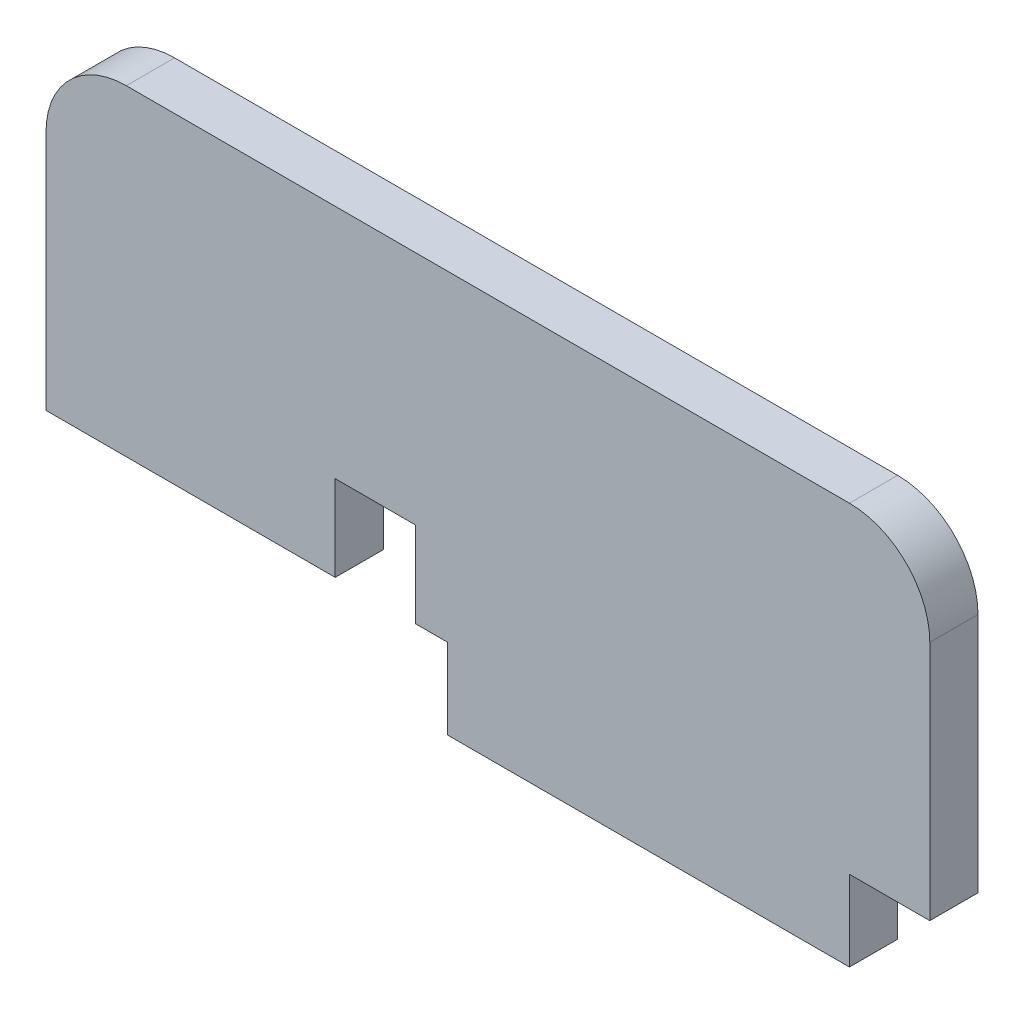
SolidWorks part; units mm, degrees
ref_plane "Plano frontal" through (0, 0, 0) normal (0, 0, 1) x (1, 0, 0)
ref_plane "Plano superior" through (0, 0, 0) normal (0, 1, 0) x (1, 0, 0)
ref_plane "Plano direito" through (0, 0, 0) normal (1, 0, 0) x (0, 0, -1)
sketch "Esboço1" plane through (0, 0, 0) normal (0, 0, 1) x (1, 0, 0)
  line L0 (-7.9412, 1.3698) -> (-2.9412, 1.3698)
  line L1 (-52.9412, 21.3698) -> (-7.9412, 21.3698)
  line L2 (-57.9412, 16.3698) -> (-57.9412, 1.3698)
  line L3 (-57.9412, 1.3698) -> (-32.9412, 1.3698)
  line L4 (-2.9412, 16.3698) -> (-2.9412, 1.3698)
  line L6 (-32.9412, 1.3698) -> (-32.9412, -3.6302)
  line L7 (-32.9412, -3.6302) -> (-7.9412, -3.6302)
  line L8 (-7.9412, 1.3698) -> (-7.9412, -3.6302)
  arc A0 (-7.9412, 21.3698) -> (-2.9412, 16.3698) centre (-7.9412, 16.3698) cw
  arc A1 (-52.9412, 21.3698) -> (-57.9412, 16.3698) centre (-52.9412, 16.3698) ccw
  point P10 (-2.9412, 21.3698)
  point P13 (-57.9412, 21.3698)
  dimension "D6" = 5
  dimension "D1" = 20
  dimension "D2" = 55
  dimension "D3" = 5
  dimension "D4" = 25
  dimension "D5" = 25
extrude "Ressalto-extrusão1" add sketch "Esboço1" along normal blind 3
sketch "Esboço3" plane through (0, 0, 3) normal (0, 0, 1) x (1, 0, 0)
  line L0 (-57.9412, 1.3698) -> (-32.9412, 1.3698) construction
  line L1 (-39.9412, 1.3698) -> (-34.9412, 1.3698)
  line L2 (-39.9412, 1.3698) -> (-39.9412, 6.6919)
  line L3 (-39.9412, 6.6919) -> (-34.9412, 6.6919)
  line L4 (-34.9412, 1.3698) -> (-34.9412, 6.6919)
  dimension "D1" = 5
  dimension "D2" = 2
extrude "Corte-extrusão2" cut sketch "Esboço3" against normal through all
